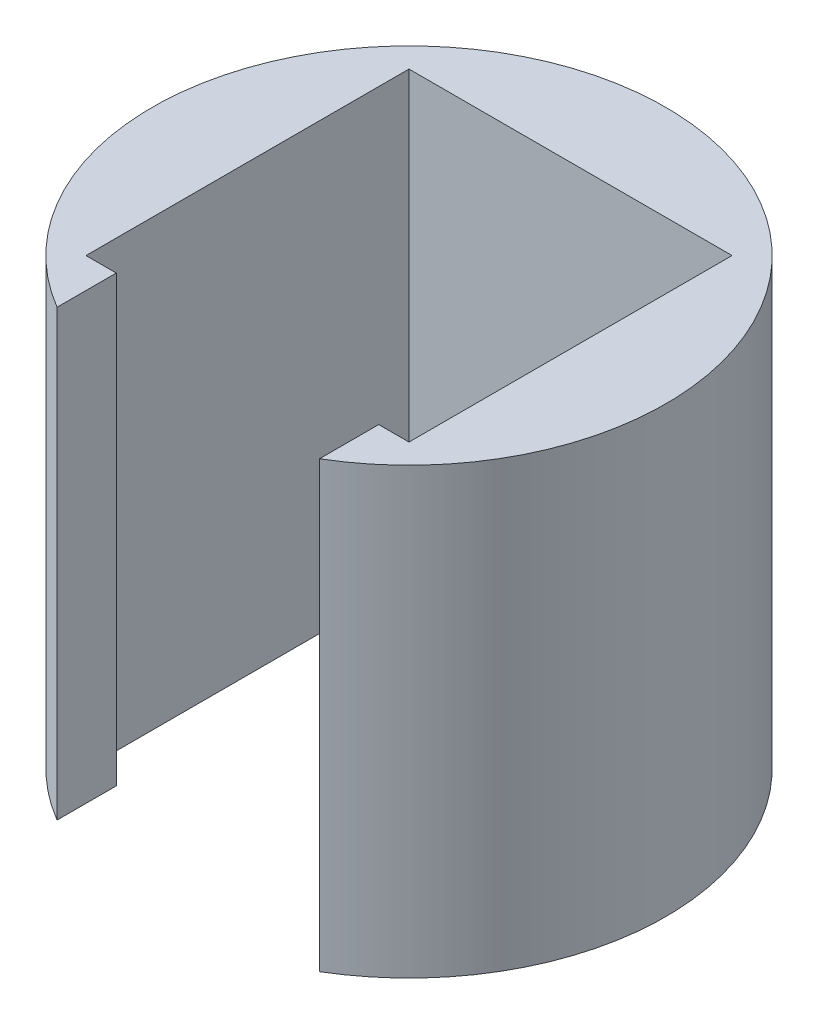
SolidWorks part; units mm, degrees
ref_plane "Front Plane" through (0, 0, 0) normal (0, 0, 1) x (1, 0, 0)
ref_plane "Top Plane" through (0, 0, 0) normal (0, 1, 0) x (1, 0, 0)
ref_plane "Right Plane" through (0, 0, 0) normal (1, 0, 0) x (0, 0, -1)
sketch "Sketch2" plane through (0, 0, 0) normal (0, 1, 0) x (1, 0, 0)
  line L0 (-8, -8) -> (-6.5, -8)
  line L1 (-8, 8) -> (8, 8)
  line L2 (-8, 8) -> (-8, -8)
  line L3 (-8, -8) -> (8, -8)
  line L4 (8, 8) -> (8, -8)
  line L5 (-8, 8) -> (8, -8) construction
  line L6 (-8, -8) -> (8, 8) construction
  line L7 (-6.5, -8) -> (-6.5, -10.9338)
  line L9 (6.5, -10.9338) -> (6.5, -8)
  line L10 (6.5, -8) -> (8, -8)
  arc A0 (6.5, -10.9338) -> (-6.5, -10.9338) centre (0, 0) ccw
extrude "Boss-Extrude3" add sketch "Sketch2" along normal blind 22 contours L9 A0 L7 L0 L2 L1 L4 L3
